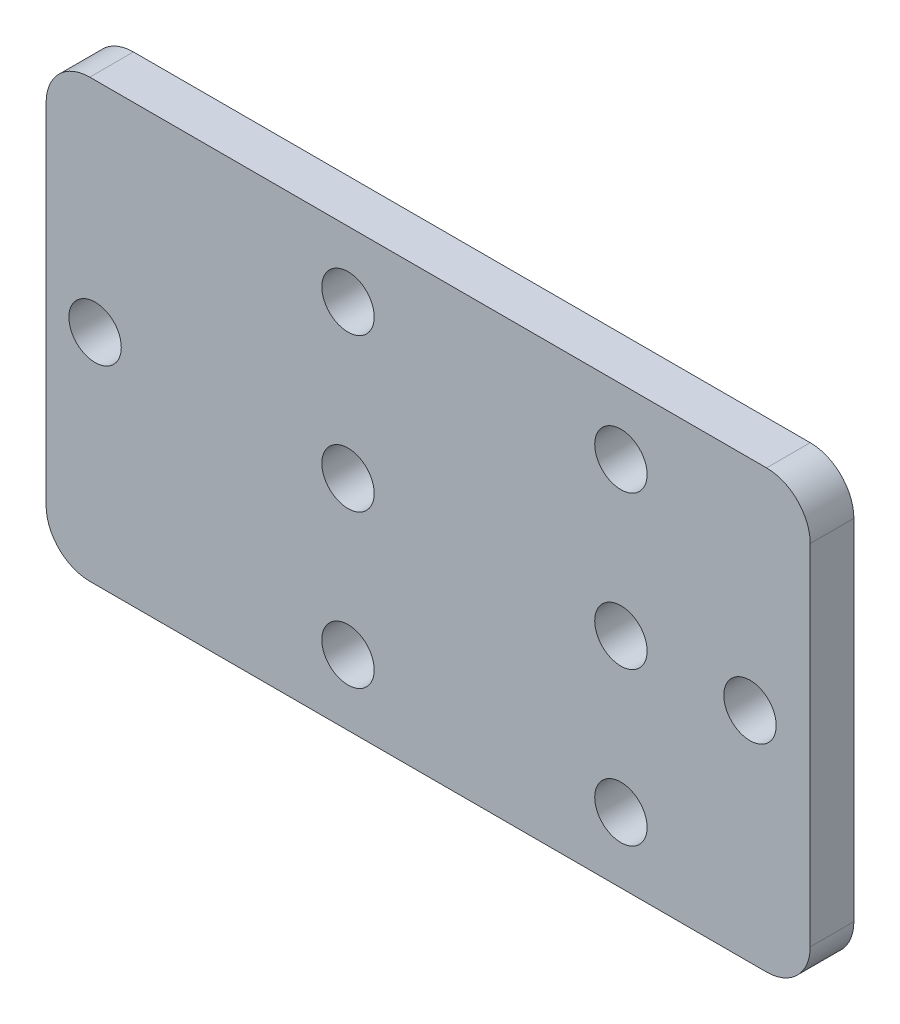
SolidWorks part; units mm, degrees
ref_plane "Front Plane" through (0, 0, 0) normal (0, 0, 1) x (1, 0, 0)
ref_plane "Top Plane" through (0, 0, 0) normal (0, 1, 0) x (1, 0, 0)
ref_plane "Right Plane" through (0, 0, 0) normal (1, 0, 0) x (0, 0, -1)
sketch "Sketch1" plane through (0, 0, 0) normal (0, 0, 1) x (1, 0, 0)
  line L1 (-5.08, -15.8896) -> (39.37, -15.8896)
  line L2 (-5.08, -15.8896) -> (-5.08, -41.2896)
  line L3 (-5.08, -41.2896) -> (39.37, -41.2896)
  line L4 (39.37, -15.8896) -> (39.37, -41.2896)
  line L5 (-5.08, -28.5896) -> (39.37, -28.5896) construction
  circle A0 centre (12.4823, -28.5896) radius 1.524
  circle A1 centre (28.3573, -28.5896) radius 1.524
  circle A2 centre (12.4823, -19.6996) radius 1.524
  circle A3 centre (28.3573, -19.6996) radius 1.524
  circle A4 centre (12.4823, -37.4796) radius 1.524
  circle A5 centre (28.3573, -37.4796) radius 1.524
  circle A6 centre (-2.2315, -28.5896) radius 1.524
  circle A7 centre (35.8685, -28.5896) radius 1.524
  dimension "D3" = 3.048
  dimension "D7" = 38.1
  dimension "D1" = 25.4
  dimension "D2" = 44.45
  dimension "D4" = 15.875
  dimension "D5" = 2
  dimension "D6" = 2
extrude "Boss-Extrude1" add sketch "Sketch1" along normal blind 2.54
fillet "Fillet1" radius 2.54 4 edges at (39.37, -41.2896, 1.27) (39.37, -15.8896, 1.27) (-5.08, -41.2896, 1.27) (-5.08, -15.8896, 1.27)
